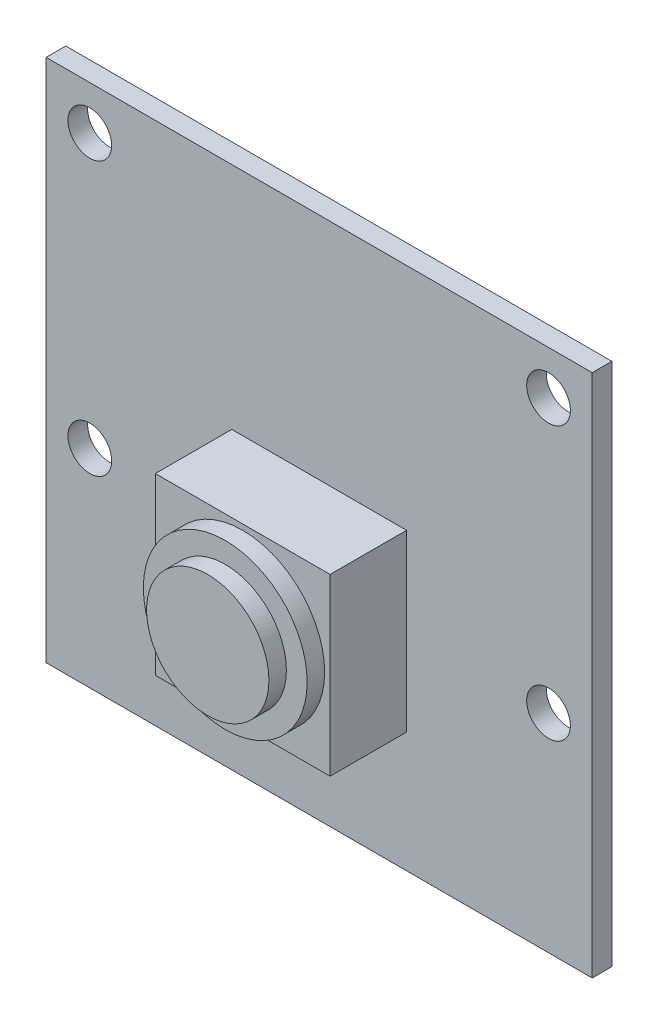
SolidWorks part; units mm, degrees
ref_plane "Alzado" through (0, 0, 0) normal (0, 0, 1) x (1, 0, 0)
ref_plane "Planta" through (0, 0, 0) normal (0, 1, 0) x (1, 0, 0)
ref_plane "Vista lateral" through (0, 0, 0) normal (1, 0, 0) x (0, 0, -1)
sketch "Croquis1" plane through (0, 0, 0) normal (0, 0, 1) x (1, 0, 0)
  line L0 (0, 0) -> (0, 12) construction
  line L1 (12.5, -12) -> (-12.5, -12)
  line L2 (12.5, -12) -> (12.5, 12)
  line L3 (12.5, 12) -> (-12.5, 12)
  line L4 (-12.5, -12) -> (-12.5, 12)
  line L5 (12.5, -12) -> (-12.5, 12) construction
  line L6 (12.5, 12) -> (-12.5, -12) construction
  line L7 (0, 12) -> (0, 10) construction
  line L8 (0, 10) -> (-10.5, 10) construction
  line L9 (0, 10) -> (10.5, 10) construction
  line L10 (10.5, 10) -> (10.5, -2.5) construction
  line L11 (10.5, -2.5) -> (-10.5, -2.5) construction
  line L12 (-10.5, -2.5) -> (-10.5, 10) construction
  circle A0 centre (10.5, 10) radius 1
  circle A1 centre (10.5, -2.5) radius 1
  circle A2 centre (-10.5, -2.5) radius 1
  circle A3 centre (-10.5, 10) radius 1
  point P0 (0, 0)
  dimension "D6" = 2
  dimension "D1" = 25
  dimension "D2" = 24
  dimension "D3" = 21
  dimension "D4" = 12.5
  dimension "D5" = 2
extrude "Saliente-Extruir1" add sketch "Croquis1" along normal blind 0.9
sketch "Croquis2" plane through (0, 0, 0.9) normal (0, 0, 1) x (1, 0, 0)
  line L0 (0, 0) -> (0, -2.5) construction
  line L2 (4, -6.5) -> (-4, -6.5)
  line L3 (4, -6.5) -> (4, 1.5)
  line L4 (4, 1.5) -> (-4, 1.5)
  line L5 (-4, -6.5) -> (-4, 1.5)
  line L6 (4, -6.5) -> (-4, 1.5) construction
  line L7 (4, 1.5) -> (-4, -6.5) construction
  line L8 (-12.5, -12) -> (12.5, -12) construction
  dimension "D1" = 8
  dimension "D2" = 5.5
extrude "Saliente-Extruir2" add sketch "Croquis2" along normal blind 3.5
sketch "Croquis3" plane through (0, 0, 4.4) normal (0, 0, 1) x (1, 0, 0)
  line L0 (-4, 1.5) -> (4, -6.5) construction
  circle A0 centre (0, -2.5) radius 3.75
  dimension "D1" = 7.5
extrude "Saliente-Extruir3" add sketch "Croquis3" along normal blind 0.8
sketch "Croquis4" plane through (0, 0, 5.2) normal (0, 0, 1) x (1, 0, 0)
  circle A0 centre (0, -2.5) radius 2.8
  dimension "D1" = 5.6
extrude "Saliente-Extruir4" add sketch "Croquis4" along normal blind 0.8
